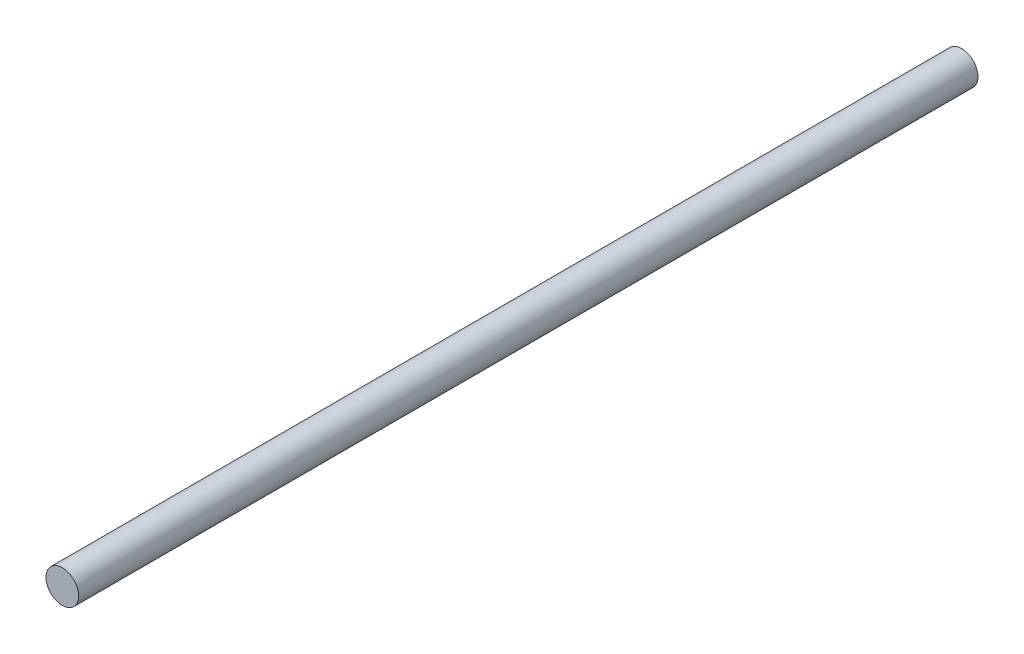
SolidWorks part; units mm, degrees
ref_plane "Front Plane" through (0, 0, 0) normal (0, 0, 1) x (1, 0, 0)
ref_plane "Top Plane" through (0, 0, 0) normal (0, 1, 0) x (1, 0, 0)
ref_plane "Right Plane" through (0, 0, 0) normal (1, 0, 0) x (0, 0, -1)
sketch "Sketch1" plane through (0, 0, 0) normal (0, 0, 1) x (1, 0, 0)
  circle A0 centre (0, 0) radius 4
  dimension "D1" = 8
extrude "Boss-Extrude1" add sketch "Sketch1" along normal blind 220
